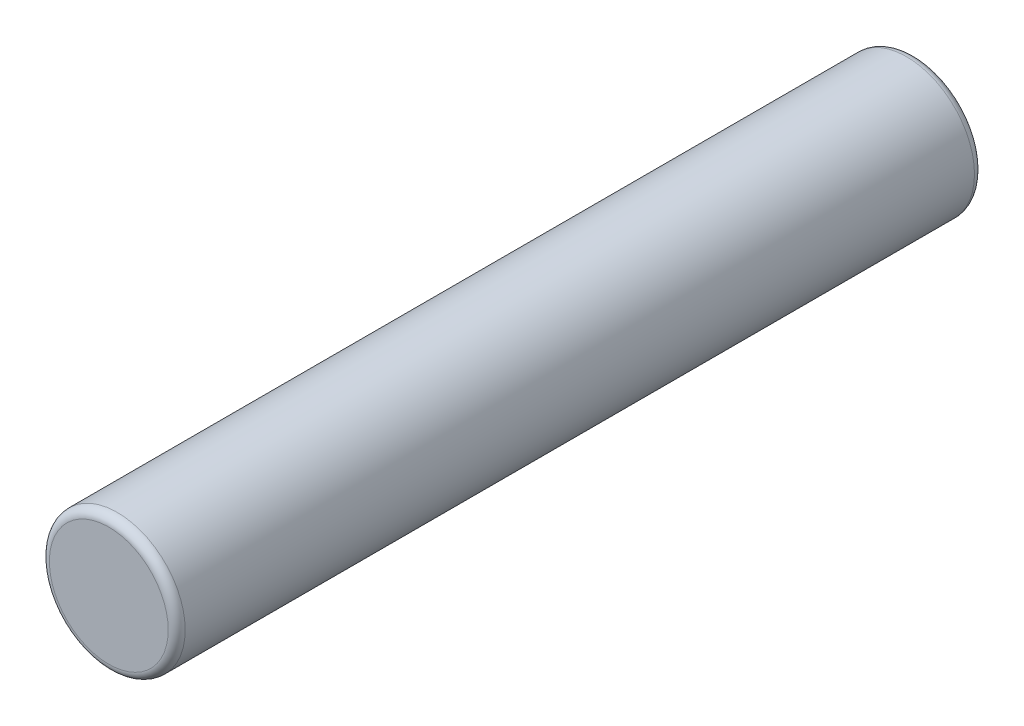
SolidWorks part; units mm, degrees
ref_plane "Front Plane" through (0, 0, 0) normal (0, 0, 1) x (1, 0, 0)
ref_plane "Top Plane" through (0, 0, 0) normal (0, 1, 0) x (1, 0, 0)
ref_plane "Right Plane" through (0, 0, 0) normal (1, 0, 0) x (0, 0, -1)
sketch "Sketch1" plane through (0, 0, 0) normal (0, 0, 1) x (1, 0, 0)
  circle A0 centre (0, 0) radius 0.8
  dimension "D1" = 1.6
extrude "Boss-Extrude2" add sketch "Sketch1" along normal blind 9.5
fillet "Fillet2" radius 0.1 2 edges at (0.8, 0, 0) (0.8, 0, 9.5)
